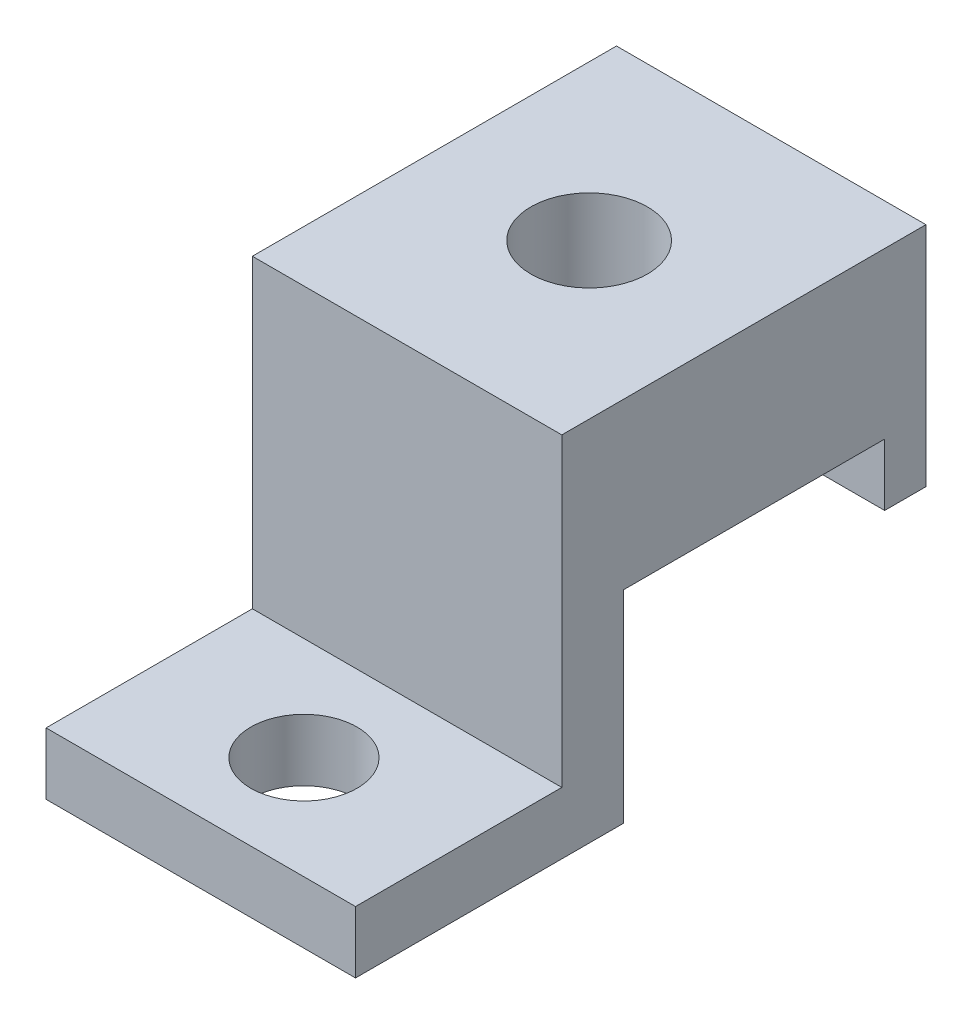
SolidWorks part; units mm, degrees
ref_plane "Alzado" through (0, 0, 0) normal (0, 0, 1) x (1, 0, 0)
ref_plane "Planta" through (0, 0, 0) normal (0, 1, 0) x (1, 0, 0)
ref_plane "Vista lateral" through (0, 0, 0) normal (1, 0, 0) x (0, 0, -1)
sketch "Croquis2" plane through (0, 0, 0) normal (1, 0, 0) x (0, 0, -1)
  line L0 (0, 0) -> (13, 0)
  line L1 (13, 0) -> (13, 9.8)
  line L2 (13, 9.8) -> (25.65, 9.8)
  line L3 (25.65, 9.8) -> (25.65, 12.8)
  line L4 (25.65, 12.8) -> (10, 12.8)
  line L5 (10, 12.8) -> (10, 3)
  line L6 (10, 3) -> (0, 3)
  line L7 (0, 3) -> (0, 0)
  dimension "D1" = 12.65
  dimension "D2" = 3
  dimension "D3" = 3
  dimension "D4" = 3
  dimension "D5" = 10
  dimension "D6" = 9.8
extrude "Saliente-Extruir1" add sketch "Croquis2" along normal blind 15
sketch "Croquis4" plane through (0, 0, 0) normal (1, 0, 0) x (0, 0, -1)
  line L0 (13, 9.8) -> (25.65, 9.8) construction
  line L1 (25.65, 12.8) -> (27.65, 12.8)
  line L2 (25.65, 12.8) -> (25.65, 6.8)
  line L3 (25.65, 6.8) -> (27.65, 6.8)
  line L4 (27.65, 12.8) -> (27.65, 6.8)
  dimension "D1" = 2
  dimension "D2" = 3
extrude "Saliente-Extruir2" add sketch "Croquis4" along normal through all
sketch "Croquis5" plane through (0, 3, 0) normal (0, 1, 0) x (1, 0, 0)
  line L0 (0, 0) -> (15, 10) construction
  circle A0 centre (7.5, 5) radius 2.575
  dimension "D1" = 5.15
extrude "Cortar-Extruir1" cut sketch "Croquis5" against normal through all
sketch "Croquis6" plane through (15, 0, 0) normal (1, 0, 0) x (0, 0, -1)
  line L1 (10, 12.8) -> (27.65, 12.8)
  line L2 (10, 12.8) -> (10, 17.8)
  line L3 (10, 17.8) -> (27.65, 17.8)
  line L4 (27.65, 12.8) -> (27.65, 17.8)
  dimension "D1" = 5
extrude "Saliente-Extruir3" add sketch "Croquis6" against normal up to surface (15 mm away) up to face at (0, 6.63, -14.6275)
sketch "Croquis7" plane through (0, 17.8, 0) normal (0, 1, 0) x (1, 0, 0)
  line L0 (7.5, 18.825) -> (15, 18.825) construction
  line L1 (15, 27.65) -> (15, 10) construction
  line L2 (7.5, 27.65) -> (7.5, 18.825) construction
  line L3 (0, 27.65) -> (15, 27.65) construction
  circle A0 centre (7.5, 18.825) radius 2.825
  dimension "D1" = 5.65
extrude "Cortar-Extruir2" cut sketch "Croquis7" against normal blind 5
sketch "Croquis8" plane through (0, 12.8, 0) normal (0, 1, 0) x (1, 0, 0)
  circle A0 centre (7.5, 18.825) radius 1.75
  dimension "D1" = 3.5
extrude "Cortar-Extruir3" cut sketch "Croquis8" against normal through all
